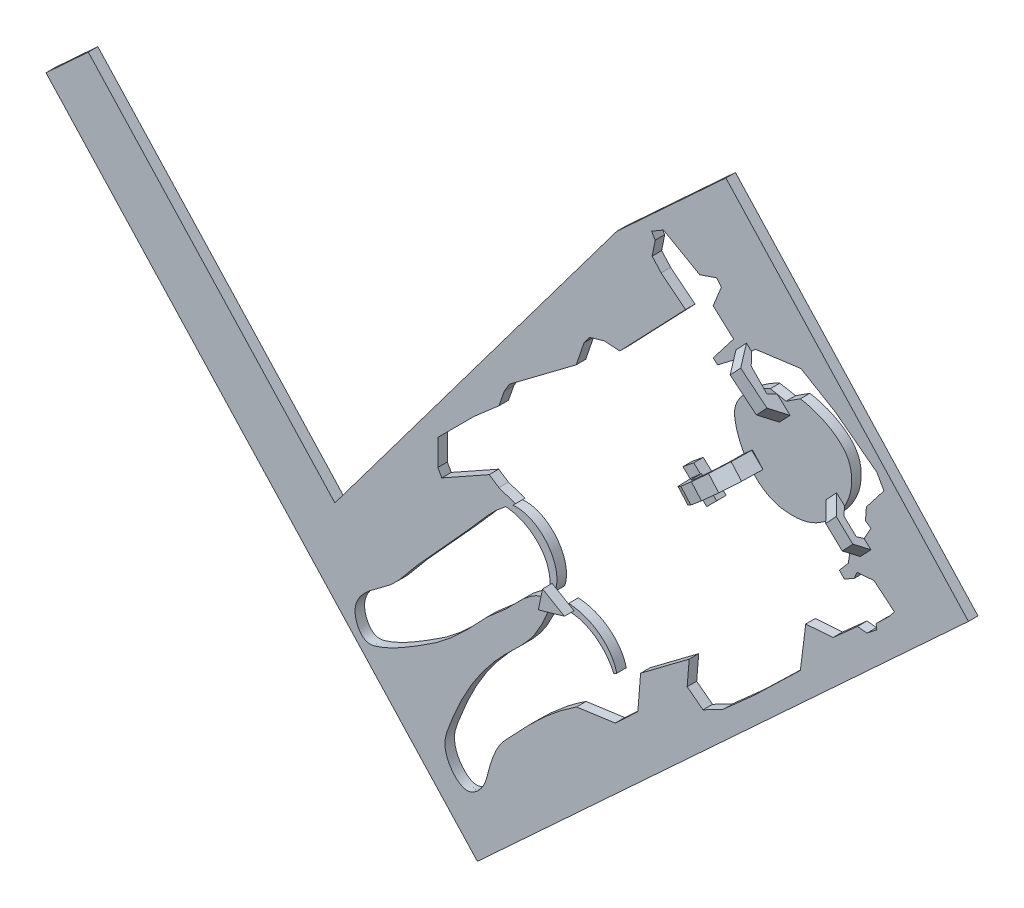
SolidWorks part; units mm, degrees
ref_plane "Front Plane" through (0, 0, 0) normal (0, 0, 1) x (1, 0, 0)
ref_plane "Top Plane" through (0, 0, 0) normal (0, 1, 0) x (1, 0, 0)
ref_plane "Right Plane" through (0, 0, 0) normal (1, 0, 0) x (0, 0, -1)
sketch "Sketch2" plane through (0, 0, 0) normal (0, 0, 1) x (1, 0, 0)
  line L0 (1286.0232, -56.9405) -> (1882.7588, -2283.9879) construction
  line L76 (26.9226, 113.4294) -> (103.2086, 30.7954)
  line L77 (103.2086, 30.7954) -> (-51.2256, -111.775)
  line L78 (-51.2256, -111.775) -> (-127.5116, -29.141)
  line L79 (-127.5116, -29.141) -> (26.9226, 113.4294)
  point P123 (103.2086, 30.7954)
  point P124 (-127.5116, -29.141)
  point P131 (0, 0)
  point P133 (0, 0)
sketch "Sketch1" plane through (0, 0, 0) normal (0, 0, 1) x (1, 0, 0)
  line L0 (1286.0232, -56.9405) -> (1882.7588, -2283.9879) construction
  line L1 (-28.49, -25.7426) -> (-26.7779, -26.002)
  line L2 (-40.0071, -9.1413) -> (-39.255, -8.3894)
  line L3 (-39.255, -8.3894) -> (-44.4458, -6.5785)
  line L4 (-44.4458, -6.5785) -> (-47.5, -4.5759)
  line L5 (-47.5, -4.5759) -> (-62.4189, -12.9285)
  line L6 (-62.4189, -12.9285) -> (-63.66, -10.7116)
  line L7 (-63.66, -10.7116) -> (-63.66, -2.5008)
  line L8 (-63.66, -2.5008) -> (-52.2159, 8.9401)
  line L9 (-52.2159, 8.9401) -> (-44.4458, 15.6954)
  line L10 (-44.4458, 15.6954) -> (-42.7631, 20.5189)
  line L11 (-42.7631, 20.5189) -> (-41.1969, 23.1953)
  line L12 (-41.1969, 23.1953) -> (-20.1451, 38.9994)
  line L13 (-20.1451, 38.9994) -> (-17.6968, 46.2435)
  line L14 (-17.6968, 46.2435) -> (-15.9523, 48.5861)
  line L15 (-15.9523, 48.5861) -> (-11.367, 49.9318)
  line L16 (-11.367, 49.9318) -> (-6.4327, 49.6327)
  line L17 (-6.4327, 49.6327) -> (14.2413, 71.2492)
  line L18 (14.2413, 71.2492) -> (6.559, 77.395)
  line L19 (6.559, 77.395) -> (3.73, 80.5482)
  line L20 (3.73, 80.5482) -> (4.6788, 85.3652)
  line L21 (4.6788, 85.3652) -> (3.584, 87.2628)
  line L22 (3.584, 87.2628) -> (7.3062, 89.4523)
  line L23 (7.3062, 89.4523) -> (18.6919, 82.9567)
  line L24 (18.6919, 82.9567) -> (24.0198, 84.7813)
  line L25 (24.0198, 84.7813) -> (25.4795, 82.9567)
  line L26 (25.4795, 82.9567) -> (22.925, 76.607)
  line L27 (22.925, 76.607) -> (29.3477, 70.7682)
  line L28 (29.3477, 70.7682) -> (22.925, 62.4479)
  line L29 (22.925, 62.4479) -> (24.3117, 61.2072)
  line L30 (24.3117, 61.2072) -> (29.2747, 65.0024)
  line L31 (29.2747, 65.0024) -> (36.2083, 71.4251)
  line L32 (36.2083, 71.4251) -> (50.5133, 73.3227)
  line L33 (50.5133, 73.3227) -> (61.4091, 66.8511)
  line L34 (61.4091, 66.8511) -> (74.4092, 57.0112)
  line L35 (74.4092, 57.0112) -> (76.6358, 53.0609)
  line L36 (76.6358, 53.0609) -> (71.1053, 45.9503)
  line L37 (71.1053, 45.9503) -> (70.818, 41.9999)
  line L38 (70.818, 41.9999) -> (72.5418, 40.8508)
  line L39 (72.5418, 40.8508) -> (68.7351, 33.9556)
  line L40 (68.7351, 33.9556) -> (67.0113, 33.0937)
  line L41 (67.0113, 33.0937) -> (65.1439, 33.0937)
  line L42 (65.1439, 33.0937) -> (64.6411, 32.4473)
  line L43 (64.6411, 32.4473) -> (65.8622, 30.7954)
  line L44 (65.8622, 30.7954) -> (65.4255, 27.7499)
  line L45 (65.4255, 27.7499) -> (62.6095, 24.4646)
  line L46 (62.6095, 24.4646) -> (64.1808, 22.8078)
  line L47 (64.1808, 22.8078) -> (67.3185, 24.5946)
  line L48 (67.3185, 24.5946) -> (68.1465, 26.6428)
  line L49 (68.1465, 26.6428) -> (73.5066, 27.0785)
  line L50 (73.5066, 27.0785) -> (79.9127, 21.762)
  line L51 (79.9127, 21.762) -> (78.3003, 19.7138)
  line L52 (78.3003, 19.7138) -> (74.1603, 15.7045)
  line L53 (74.1603, 15.7045) -> (74.3782, 14.0921)
  line L54 (74.3782, 14.0921) -> (71.3277, 11.6953)
  line L55 (71.3277, 11.6953) -> (68.2772, 11.9568)
  line L56 (68.2772, 11.9568) -> (60.6074, 5.115)
  line L57 (60.6074, 5.115) -> (52.0224, 4.5049)
  line L58 (52.0224, 4.5049) -> (50.3453, -8.9701)
  line L59 (50.3453, -8.9701) -> (35.9251, -22.9079)
  line L60 (35.9251, -22.9079) -> (25.9784, -31.769)
  line L61 (25.9784, -31.769) -> (19.727, -35.0133)
  line L62 (19.727, -35.0133) -> (14.7418, -31.215)
  line L63 (14.7418, -31.215) -> (15.3748, -23.381)
  line L64 (15.3748, -23.381) -> (0.1025, -34.8551)
  line L65 (0.1025, -34.8551) -> (-0.768, -45.7752)
  line L66 (-0.768, -45.7752) -> (-7.8898, -52.4222)
  line L67 (-7.8898, -52.4222) -> (-20.0495, -54.1148)
  line L68 (-22.5273, -27.1558) -> (-23.4061, -29.2415)
  line L69 (-8.3278, -39.1352) -> (-7.4028, -38.6278)
  line L70 (16.8098, 30.7954) -> (24.0198, 24.0409)
  line L71 (24.0198, 24.0409) -> (20.8957, 20.9027)
  line L72 (20.8957, 20.9027) -> (13.4163, 28.0634)
  line L73 (13.4163, 28.0634) -> (16.8098, 30.7954)
  line L74 (40.8941, 63.0406) -> (45.8421, 62.0938)
  line L75 (45.8421, 62.0938) -> (50.3453, 65.0024)
  spline S0 degree 3 poles (-20.0495, -54.1148) (-26.6388, -58.3691) (-33.6008, -64.7531) (-40.7762, -72.6682) (-43.9814, -75.8387) (-46.0828, -79.9264) (-47.8139, -85.1938) (-48.7891, -90.8299) (-54.6555, -95.6518) (-60.5056, -90.4093) (-61.9056, -84.9179) (-60.5137, -80.2452) (-58.3945, -74.9837) (-53.5425, -64.1946) (-44.8773, -52.6271) (-32.7097, -42.1777) (-29.3444, -33.6017) (-27.4286, -29.2415) knots 0 0 0 0 0.177151 0.212775 0.242683 0.278781 0.315571 0.368258 0.408422 0.457109 0.511388 0.531457 0.566383 0.640421 0.799023 0.88992 1 1 1 1
  spline S1 degree 3 poles (-27.4286, -29.2415) (-29.7661, -28.7381) (-35.8431, -31.1244) (-40.9759, -37.8993) (-47.6635, -42.8911) (-54.1329, -50.2314) (-61.9413, -57.5783) (-72.4988, -63.965) (-79.2955, -68.0353) (-87.3455, -70.4613) (-91.2876, -62.2394) (-86.028, -54.9055) (-77.6228, -50.3161) (-71.0875, -41.3709) (-61.9407, -31.5386) (-52.3911, -21.1891) (-45.8482, -13.2933) (-42.3526, -10.7116) knots 0 0 0 0 0.046259 0.121306 0.166363 0.211467 0.315557 0.378654 0.454548 0.479099 0.531003 0.580272 0.646093 0.719897 0.796613 0.914199 1 1 1 1
  spline S2 degree 3 poles (-42.3526, -10.7116) (-34.8729, -11.1269) (-27.5299, -17.6413) (-28.49, -25.7426) knots 0 0 0 0 1 1 1 1
  spline S3 degree 3 poles (-26.7779, -26.002) (-24.018, -18.1063) (-31.5481, -8.362) (-40.0071, -9.1413) knots 0 0 0 0 1 1 1 1
  spline S4 degree 3 poles (-22.5273, -27.1558) (-15.8559, -27.335) (-8.9905, -31.9836) (-7.4028, -38.6278) knots 0 0 0 0 1 1 1 1
  spline S5 degree 3 poles (-23.4061, -29.2415) (-16.8915, -28.8429) (-10.8663, -33.3867) (-8.3278, -39.1352) knots 0 0 0 0 1 1 1 1
  spline S6 degree 3 poles (50.3453, 65.0024) (55.7068, 64.1604) (65.0131, 60.3569) (66.7443, 50.9649) (65.9646, 45.2385) (61.5953, 38.0574) (54.9719, 32.6302) (47.3606, 31.7067) (40.2861, 32.7993) (33.3675, 38.8689) (30.1851, 45.8665) (28.8736, 55.9829) (36.6466, 61.192) (40.8941, 63.0406) knots 0 0 0 0 0.194847 0.224841 0.288104 0.367004 0.479066 0.534322 0.598079 0.692933 0.801566 0.828048 1 1 1 1
  point P123 (103.2086, 30.7954)
  point P124 (-127.5116, -29.141)
  point P131 (0, 0)
  point P133 (0, 0)
extrude "Boss-Extrude1" add sketch "Sketch2" along normal blind 3
extrude "Cut-Extrude2" cut sketch "Sketch1" along normal through all
sketch "Sketch3" plane through (0, 0, 3) normal (0, 0, 1) x (1, 0, 0)
  line L0 (-27.7386, -24.3141) -> (-20.8491, -28.3284)
  line L1 (-20.8491, -28.3284) -> (-29.0405, -30.6611)
  line L2 (-29.0405, -30.6611) -> (-27.7386, -24.3141)
  point P2 (-20.8491, -28.3284)
  point P4 (-27.7386, -24.3141)
  point P5 (-29.0405, -30.6611)
extrude "Boss-Extrude2" add sketch "Sketch3" along normal blind 3 contours L1 L2 L0
sketch "Sketch4" plane through (0, 0, 3) normal (0, 0, 1) x (1, 0, 0)
  line L0 (33.406, 71.7215) -> (74.3277, 33.3146)
  line L1 (74.3277, 33.3146) -> (71.0105, 29.7802)
  line L2 (71.0105, 29.7802) -> (30.0889, 68.1871)
  line L3 (30.0889, 68.1871) -> (33.406, 71.7215)
  line L4 (15.6766, 25.8995) -> (35.2637, 43.5643)
  line L5 (35.2637, 43.5643) -> (38.5961, 39.8693)
  line L6 (38.5961, 39.8693) -> (19.0302, 22.6887)
  line L7 (19.0302, 22.6887) -> (15.6766, 25.8995)
  line L8 (13.4163, 28.0634) -> (20.8957, 20.9027) construction
  point P8 (19.2296, 22.9982)
  point P9 (15.6766, 25.8995)
  point P12 (19.0302, 22.6887)
  point P13 (38.5961, 39.8693)
extrude "Boss-Extrude3" add sketch "Sketch4" along normal blind 10
sketch "Sketch5" plane through (-2.9641, 3.3757, 0) normal (0.6598, -0.7514, 0) x (0.7514, 0.6598, 0)
  line L0 (33.6892, 3) -> (34.7056, 7.1188)
  line L1 (34.7056, 7.1188) -> (40.0674, 10.3582)
  line L2 (40.0674, 10.3582) -> (46.1505, 10.3582)
  line L3 (46.1505, 10.3582) -> (50.8445, 7.4757)
  line L4 (50.8445, 7.4757) -> (51.3695, 3)
  line L5 (51.3695, 3) -> (55.3085, 3) construction
  line L6 (33.6892, 3) -> (51.3695, 3) construction
  line L7 (29.2702, 3) -> (31.242, 8.5743)
  line L8 (31.242, 8.5743) -> (37.1871, 12.0877)
  line L9 (37.1871, 12.0877) -> (42.8629, 13)
  line L10 (29.2702, 13) -> (55.3085, 13) construction
  line L11 (42.8629, 13) -> (48.8948, 12.0877)
  line L12 (48.8948, 12.0877) -> (53.7479, 8.5743)
  line L13 (53.7479, 8.5743) -> (55.3085, 3)
  line L14 (33.6892, 3) -> (51.3695, 3)
  line L15 (55.3085, 3) -> (55.3085, 13)
  line L16 (55.3085, 13) -> (43.2475, 14.5164)
  line L17 (43.2475, 14.5164) -> (29.2702, 13)
  line L19 (29.2702, 13) -> (28.8687, 13)
  line L20 (28.8687, 13) -> (28.8687, 3)
  line L21 (28.8687, 13) -> (28.8687, 3) construction
  line L22 (28.8687, 3) -> (29.2702, 3)
extrude "Cut-Extrude3" cut sketch "Sketch5" against normal up to next
sketch "Sketch7" plane through (51.4338, 54.8015, 0) normal (0.6843, 0.7292, 0) x (0.7292, -0.6843, 0)
  line L0 (-24.7242, -3) -> (-20.5475, -7.8762)
  line L1 (-20.5475, -7.8762) -> (-9.9169, -7.3649)
  line L2 (-9.9169, -7.3649) -> (-5.9525, -3)
  line L3 (17.6285, -3) -> (-11.4208, -3) construction
  line L4 (18.6919, -6.4345) -> (25.8496, -6.4345)
  line L5 (14.1685, -3) -> (18.6919, -6.4345)
  line L7 (-5.9525, -3) -> (14.1685, -3)
  line L8 (-24.7242, -3) -> (-24.7242, -13)
  line L9 (-24.7242, -13) -> (31.3977, -13)
  line L10 (31.3977, -13) -> (31.3977, -3) construction
  line L11 (31.3977, -13) -> (-24.7242, -13) construction
  line L12 (31.3977, -13) -> (31.3977, -3)
  line L13 (31.3977, -3) -> (28.9397, -3)
  line L14 (25.8496, -6.4345) -> (28.9397, -3)
  line L15 (17.6285, -3) -> (19.387, -4.5822)
  line L16 (19.387, -4.5822) -> (24.8353, -4.5822)
  line L17 (24.8353, -4.5822) -> (26.0259, -3)
  line L18 (26.0259, -3) -> (17.6285, -3) construction
  line L19 (31.3977, -3) -> (26.0259, -3) construction
  line L20 (26.0259, -3) -> (17.6285, -3)
  line L21 (-22.5973, -3) -> (-19.7359, -5.1532)
  line L22 (-19.7359, -5.1532) -> (-12.6973, -5.3953)
  line L23 (-12.6973, -5.3953) -> (-11.4208, -3)
  line L24 (-11.4208, -3) -> (-22.5973, -3)
extrude "Cut-Extrude4" cut sketch "Sketch7" against normal up to next
sketch "Sketch8" plane through (0, 0, 3) normal (0, 0, 1) x (1, 0, 0)
  line L9 (-7.414, 81.7306) -> (-107.0745, -51.2788)
  line L10 (26.9226, 113.4294) -> (-127.5116, -29.141) construction
  line L11 (-127.5116, -29.141) -> (-51.2256, -111.775) construction
  line L12 (-107.0745, -51.2788) -> (-127.5116, -29.141)
  line L13 (-127.5116, -29.141) -> (-7.414, 81.7306)
  point P4 (-107.0745, -51.2788)
extrude "Cut-Extrude5" cut sketch "Sketch8" against normal up to next
sketch "Sketch9" plane through (0, 0, 0) normal (0, 0, 1) x (1, 0, 0)
  line L0 (-107.0745, -51.2788) -> (-186.8897, 35.1782)
  line L1 (-186.8897, 35.1782) -> (-173.5877, 47.4583)
  line L2 (-173.5877, 47.4583) -> (-96.0361, -36.5466)
  line L3 (-107.0745, -51.2788) -> (-7.414, 81.7306) construction
  line L4 (-96.0361, -36.5466) -> (-107.0745, -51.2788)
  line L5 (-107.0745, -51.2788) -> (-51.2256, -111.775) construction
  line L6 (-51.2256, -111.775) -> (103.2086, 30.7954) construction
  point P11 (0, 0)
  dimension "D1" = 200
extrude "Boss-Extrude4" add sketch "Sketch9" along normal blind 3
